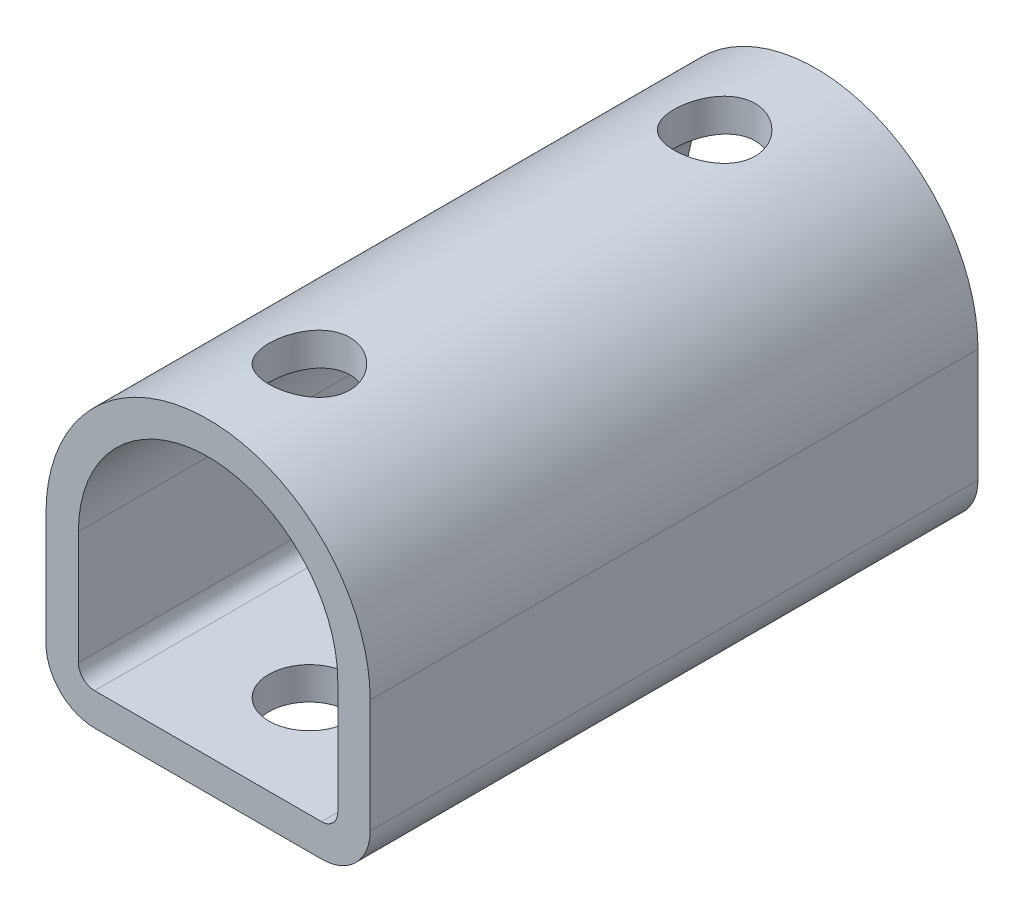
SolidWorks part; units mm, degrees
ref_plane "Élévation" through (0, 0, 0) normal (0, 0, 1) x (1, 0, 0)
ref_plane "Vue en plan" through (0, 0, 0) normal (0, 1, 0) x (1, 0, 0)
ref_plane "Vue latérale" through (0, 0, 0) normal (1, 0, 0) x (0, 0, -1)
sketch "Croquis1" plane through (0, 0, 0) normal (0, 0, 1) x (1, 0, 0)
  line L0 (-20, 0) -> (-20, -14)
  line L1 (-14, -20) -> (14, -20)
  line L2 (20, -14) -> (20, 0)
  line L3 (-16, 0) -> (-16, -14)
  line L4 (-14, -16) -> (14, -16)
  line L5 (16, -14) -> (16, 0)
  arc A0 (20, 0) -> (-20, 0) centre (0, 0) ccw
  arc A1 (14, -20) -> (20, -14) centre (14, -14) ccw
  arc A2 (-20, -14) -> (-14, -20) centre (-14, -14) ccw
  arc A3 (-16, -14) -> (-14, -16) centre (-14, -14) ccw
  arc A4 (14, -16) -> (16, -14) centre (14, -14) ccw
  arc A5 (16, 0) -> (-16, 0) centre (0, 0) ccw
  point P10 (-20, -20)
  dimension "D1" = 40
  dimension "D3" = 6
  dimension "D2" = 20
  dimension "D4" = 4
extrude "Saliente-Extruir1" add sketch "Croquis1" along normal mid plane 75
sketch "Esquisse2" plane through (0, 0, 0) normal (0, 1, 0) x (1, 0, 0)
  line L0 (0, 0) -> (0, -25) construction
  line L1 (0, 0) -> (0, 25) construction
hole_wizard "Perceuse à colonne pour M1.61" positions "Croquis4" profile "Croquis3" hole size "M1.6" standard "Ansi Metric" end condition through all
sketch "Croquis4" plane through (0, -20, 0) normal (0, -1, 0) x (-1, 0, 0)
  point P0 (0, -25)
  point P3 (0, 25)
sketch "Croquis3" plane through (0, -20, 25) normal (1, 0, 0) x (0, 0, -1)
  line L0 (0, 0) -> (0, 40)
  line L1 (0, 40) -> (5, 40)
  line L2 (5, 40) -> (5, 0)
  line L5 (5, 0) -> (0, 0)
  line L11 (0, -6.35) -> (0, 107.95) construction
  dimension "Diámetro de taladro hasta el siguiente" = 10
  dimension "Profundidad de taladro hasta el siguiente" = 40
